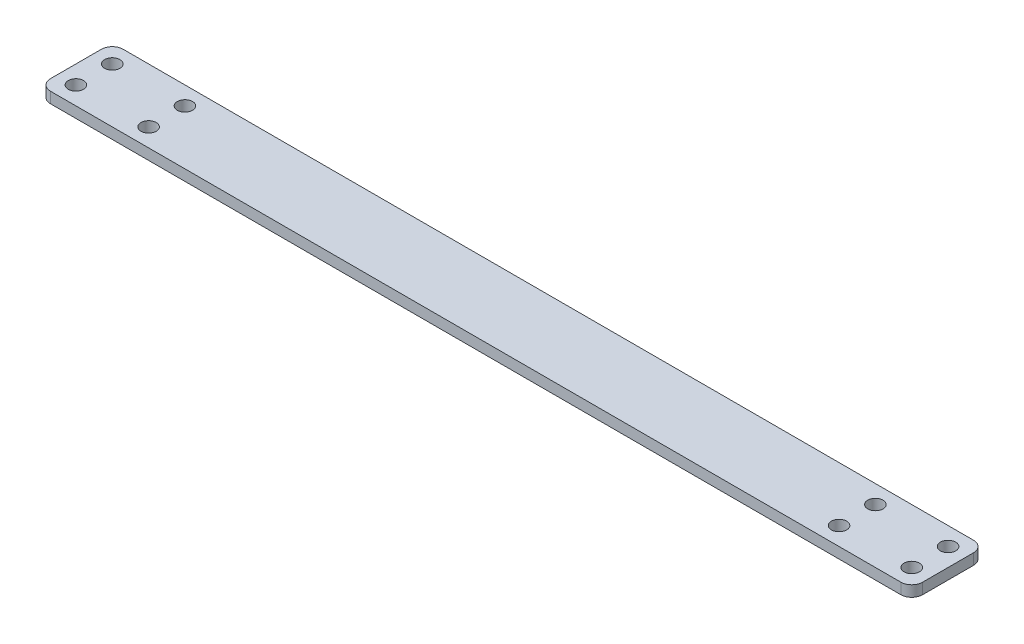
SolidWorks part; units mm, degrees
material "Hexcel AS4C (3000 丝)"
ref_plane "前视基准面" through (0, 0, 0) normal (0, 0, 1) x (1, 0, 0)
ref_plane "上视基准面" through (0, 0, 0) normal (0, 1, 0) x (1, 0, 0)
ref_plane "右视基准面" through (0, 0, 0) normal (1, 0, 0) x (0, 0, -1)
sketch "草图2" plane through (0, 0, 0) normal (0, 1, 0) x (1, 0, 0)
  line L0 (105, 0) -> (-105, 0) construction
  line L1 (0, 0) -> (0, -50000) construction
  line L2 (115, 0) -> (95, 0) construction
  line L3 (-115, 5) -> (-95, 5) construction
  line L4 (-115, 5) -> (-115, -5) construction
  line L5 (-115, -5) -> (-95, -5) construction
  line L6 (-95, 5) -> (-95, -5) construction
  line L7 (-105, -5) -> (-105, 5) construction
  line L8 (-115, 0) -> (-95, 0) construction
  line L9 (105, -5) -> (105, 5) construction
  line L10 (95, 5) -> (95, -5) construction
  line L11 (115, -5) -> (95, -5) construction
  line L12 (115, 5) -> (115, -5) construction
  line L13 (115, 5) -> (95, 5) construction
  line L15 (-120, 10) -> (120, 10)
  line L16 (-120, 10) -> (-120, -10)
  line L17 (-120, -10) -> (120, -10)
  line L18 (120, 10) -> (120, -10)
  line L19 (0, -10) -> (0, 10) construction
  line L20 (-120, 0) -> (120, 0) construction
  circle A0 centre (-115, 5) radius 2.1
  circle A1 centre (-95, 5) radius 2.1
  circle A2 centre (-95, -5) radius 2.1
  circle A3 centre (-115, -5) radius 2.1
  circle A4 centre (115, -5) radius 2.1
  circle A5 centre (95, -5) radius 2.1
  circle A6 centre (95, 5) radius 2.1
  circle A7 centre (115, 5) radius 2.1
  point P4 (0, 0)
  point P26 (0, 0)
  dimension "D4" = 4.2
  dimension "D1" = 210
  dimension "D2" = 10
  dimension "D3" = 20
  dimension "D5" = 5
  dimension "D6" = 20
extrude "凸台-拉伸1" add sketch "草图2" along normal blind 3
fillet "圆角1" radius 3 4 edges at (120, 1.5, 10) (-120, 1.5, -10) (120, 1.5, -10) (-120, 1.5, 10)
